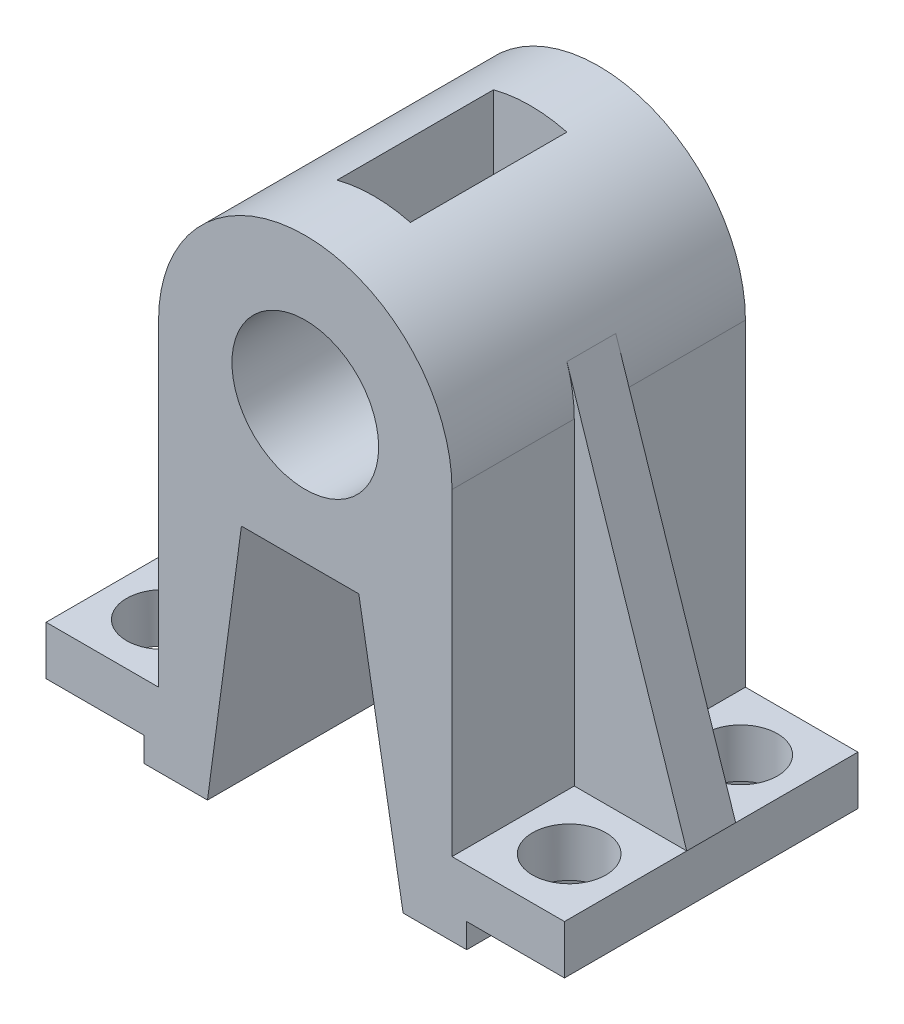
SolidWorks part; units mm, degrees
ref_plane "Front Plane" through (0, 0, 0) normal (0, 0, 1) x (1, 0, 0)
ref_plane "Top Plane" through (0, 0, 0) normal (0, 1, 0) x (1, 0, 0)
ref_plane "Right Plane" through (0, 0, 0) normal (1, 0, 0) x (0, 0, -1)
sketch "Sketch1" plane through (0, 0, 0) normal (0, 0, 1) x (1, 0, 0)
  line L1 (-30, 0) -> (-30, -65)
  line L2 (-30, -65) -> (-53, -65)
  line L3 (-53, -65) -> (-53, -75)
  line L4 (-53, -75) -> (-33, -75)
  line L5 (-33, -75) -> (-33, -80)
  line L6 (-33, -80) -> (-20, -80)
  line L7 (-20, -80) -> (-13.0562, -28)
  line L8 (-13.0562, -28) -> (10.9438, -28)
  line L9 (0, -28) -> (0, -30)
  line L10 (10.9438, -28) -> (20, -80)
  line L11 (33, -80) -> (20, -80)
  line L12 (33, -75) -> (33, -80)
  line L13 (53, -75) -> (33, -75)
  line L14 (53, -65) -> (53, -75)
  line L15 (30, -65) -> (53, -65)
  line L16 (30, 0) -> (30, -65)
  line L17 (0, -28) -> (0, -30)
  arc A0 (30, 0) -> (-30, 0) centre (0, 0) ccw
  circle A1 centre (0, 0) radius 15
  arc A2 (0, -30) -> (10.7703, -28) centre (0, 0) ccw
  dimension "D1" = 60
  dimension "D2" = 30
  dimension "D3" = 80
  dimension "D4" = 24
  dimension "D5" = 10
  dimension "D6" = 5
  dimension "D7" = 66
  dimension "D8" = 40
  dimension "D9" = 52
  dimension "D10" = 106
extrude "Boss-Extrude1" add sketch "Sketch1" along normal mid plane 60 contours L16 A0 L1 L2 L3 L4 L5 L6 L7 L8 L10 L11 L12 L13 L14 L15 A1
sketch "Sketch2" plane through (0, -65, 0) normal (0, 1, 0) x (1, 0, 0)
  circle A0 centre (41.5, 17.5381) radius 7.5
  circle A1 centre (41.5, -17.5381) radius 7.5
  point P8 (0, 0)
  dimension "D1" = 15
extrude "Cut-Extrude1" cut sketch "Sketch2" against normal blind 60
mirror "Mirror1" about plane through (0, 0, 0) normal (1, 0, 0) of "Cut-Extrude1"
sketch "Sketch3" plane through (0, 0, 0) normal (0, 1, 0) x (1, 0, 0)
  line L1 (-7.5, -16) -> (7.5, -16)
  line L2 (-7.5, -16) -> (-7.5, 16)
  line L3 (-7.5, 16) -> (7.5, 16)
  line L4 (7.5, -16) -> (7.5, 16)
  line L5 (-7.5, -16) -> (7.5, 16) construction
  line L6 (-7.5, 16) -> (7.5, -16) construction
  point P0 (0, 0)
  dimension "D1" = 15
  dimension "D2" = 32
extrude "Cut-Extrude2" cut sketch "Sketch3" along normal through all
sketch "Sketch4" plane through (0, 0, 0) normal (0, 0, 1) x (1, 0, 0)
  line L0 (-28.4936, 9.3871) -> (-53, -65)
  arc A0 (30, 0) -> (-30, 0) centre (0, 0) ccw construction
rib "Rib1" sketch "Sketch4" sketch "Sketch4" thickness 10 extrusion direction parallel to sketch draft on no parameters "D1"=10
mirror "Mirror2" about plane through (0, 0, 0) normal (1, 0, 0) of "Rib1"
